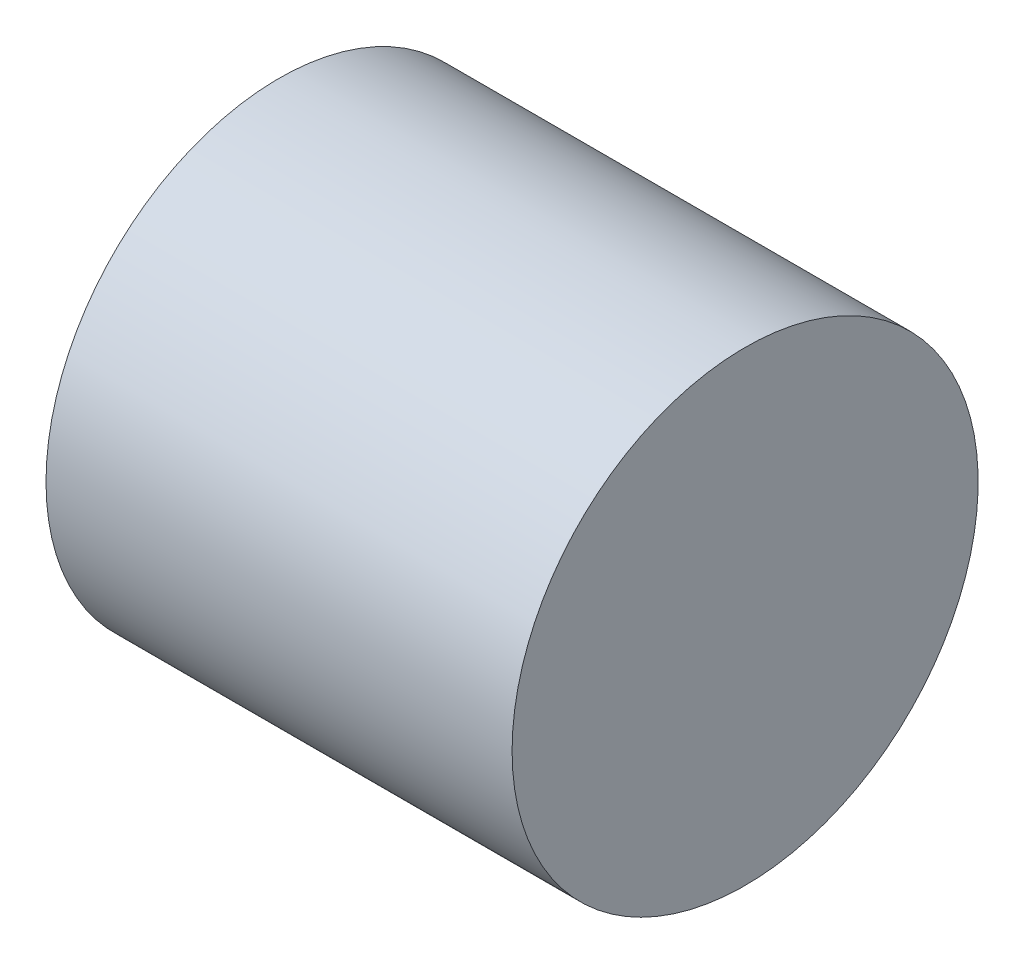
SolidWorks part; units mm, degrees
material "1023 al carbonio, lamiera (SS)"
ref_plane "Piano frontale" through (0, 0, 0) normal (0, 0, 1) x (1, 0, 0)
ref_plane "Piano superiore" through (0, 0, 0) normal (0, 1, 0) x (1, 0, 0)
ref_plane "Piano destro" through (0, 0, 0) normal (1, 0, 0) x (0, 0, -1)
sketch "Schizzo1" plane through (0, 0, 0) normal (0, 0, 1) x (1, 0, 0)
  line L1 (0, 0) -> (40, 0)
  line L2 (0, 0) -> (0, 20)
  line L3 (0, 20) -> (40, 20)
  line L4 (40, 0) -> (40, 20)
  dimension "D1" = 20
  dimension "D2" = 40
revolve "Rivoluzione1" add sketch "Schizzo1" angle 360 about L3
